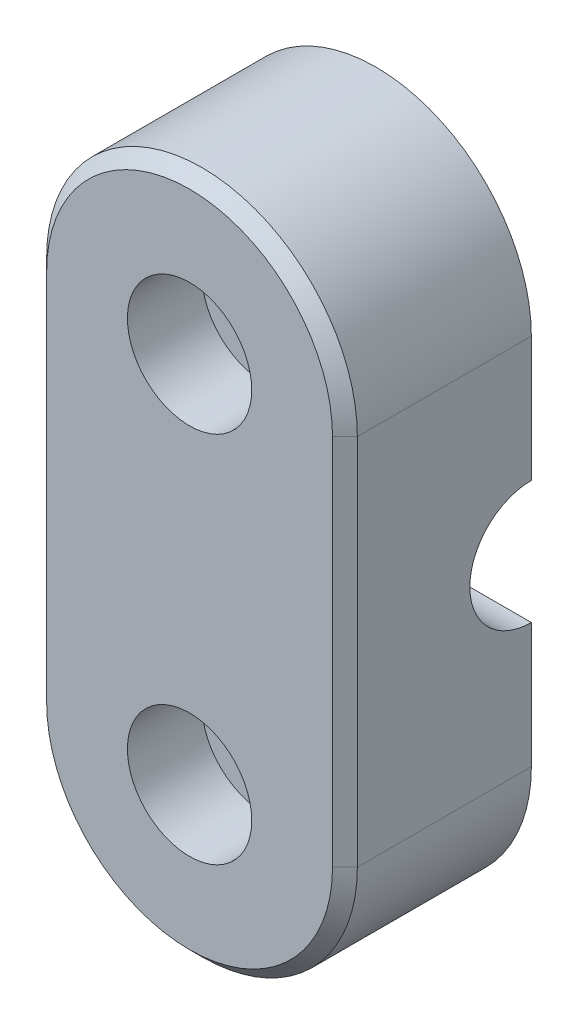
SolidWorks part; units mm, degrees
ref_plane "Front Plane" through (0, 0, 0) normal (0, 0, 1) x (1, 0, 0)
ref_plane "Top Plane" through (0, 0, 0) normal (0, 1, 0) x (1, 0, 0)
ref_plane "Right Plane" through (0, 0, 0) normal (1, 0, 0) x (0, 0, -1)
sketch "Sketch1" plane through (0, 0, 0) normal (0, 0, 1) x (1, 0, 0)
  line L12 (-12.5, 15) -> (-12.5, -15)
  line L13 (12.5, 15) -> (12.5, -15)
  arc A0 (12.5, 15) -> (-12.5, 15) centre (0, 15) ccw construction
  arc A1 (-12.5, -15) -> (12.5, -15) centre (0, -15) ccw construction
  arc A2 (12.5, 15) -> (-12.5, 15) centre (0, 15) ccw
  arc A3 (-12.5, -15) -> (12.5, -15) centre (0, -15) ccw
  circle A4 centre (0, 15) radius 3.25 construction
  circle A5 centre (0, -15) radius 3.25 construction
  circle A6 centre (0, 15) radius 3.25
  circle A7 centre (0, -15) radius 3.25
extrude "Boss-Extrude1" add sketch "Sketch1" along normal blind 15
sketch "Sketch2" plane through (12.5, 0, 0) normal (1, 0, 0) x (0, 0, -1)
  circle A0 centre (0, 0) radius 4.95
  arc A2 (0, -4.95) -> (0, 4.95) centre (0, 0) ccw construction
extrude "Cut-Extrude1" cut sketch "Sketch2" against normal up to next
chamfer "Chamfer1" distance 1 angle 45 4 edges at (-12.5, 0, 15) (12.5, 0, 15) (0, -27.5, 15) (0, 27.5, 15)
sketch "Sketch3" plane through (0, 0, 15) normal (0, 0, 1) x (1, 0, 0)
  circle A0 centre (0, 15) radius 5
  circle A1 centre (0, -15) radius 5
  dimension "D1" = 10
extrude "Cut-Extrude2" cut sketch "Sketch3" against normal blind 6
sketch "Sketch5" plane through (0, 0, 0) normal (1, 0, 0) x (0, 0, -1)
  line L0 (0, 4.95) -> (0, -4.95)
  circle A0 centre (0, 0) radius 4.95
  circle A1 centre (0, 0) radius 4.5
  arc A2 (0, -4.5) -> (0, 4.5) centre (0, 0) ccw construction
  arc A4 (0, 4.95) -> (0, -4.95) centre (0, 0) ccw construction
extrude "Boss-Extrude2" add sketch "Sketch5" along normal mid plane 1.9 contours A1 L0 A0
